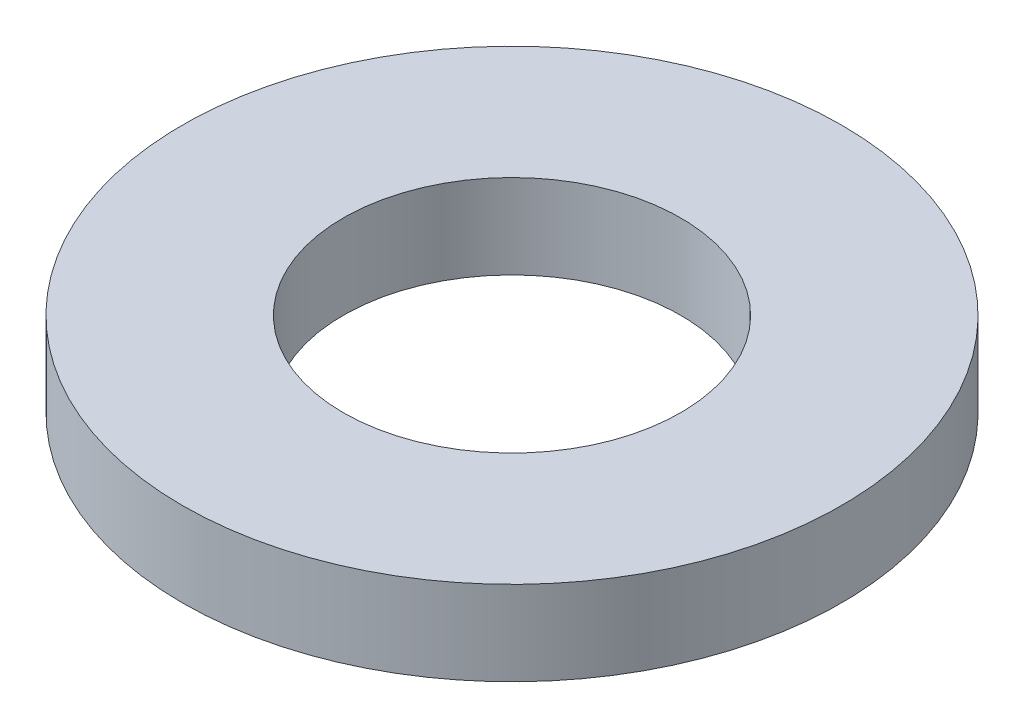
SolidWorks part; units mm, degrees
material "Polyetheretherketone (PEEK)"
ref_plane "Front Plane" through (0, 0, 0) normal (0, 0, 1) x (1, 0, 0)
ref_plane "Top Plane" through (0, 0, 0) normal (0, 1, 0) x (1, 0, 0)
ref_plane "Right Plane" through (0, 0, 0) normal (1, 0, 0) x (0, 0, -1)
sketch "Sketch1" plane through (0, 0, 0) normal (0, 1, 0) x (1, 0, 0)
  circle A0 centre (0, 0) radius 6.25
  circle A1 centre (0, 0) radius 3.2
  dimension "D1" = 12.5
  dimension "D2" = 6.4
extrude "Boss-Extrude1" add sketch "Sketch1" along normal blind 1.6
